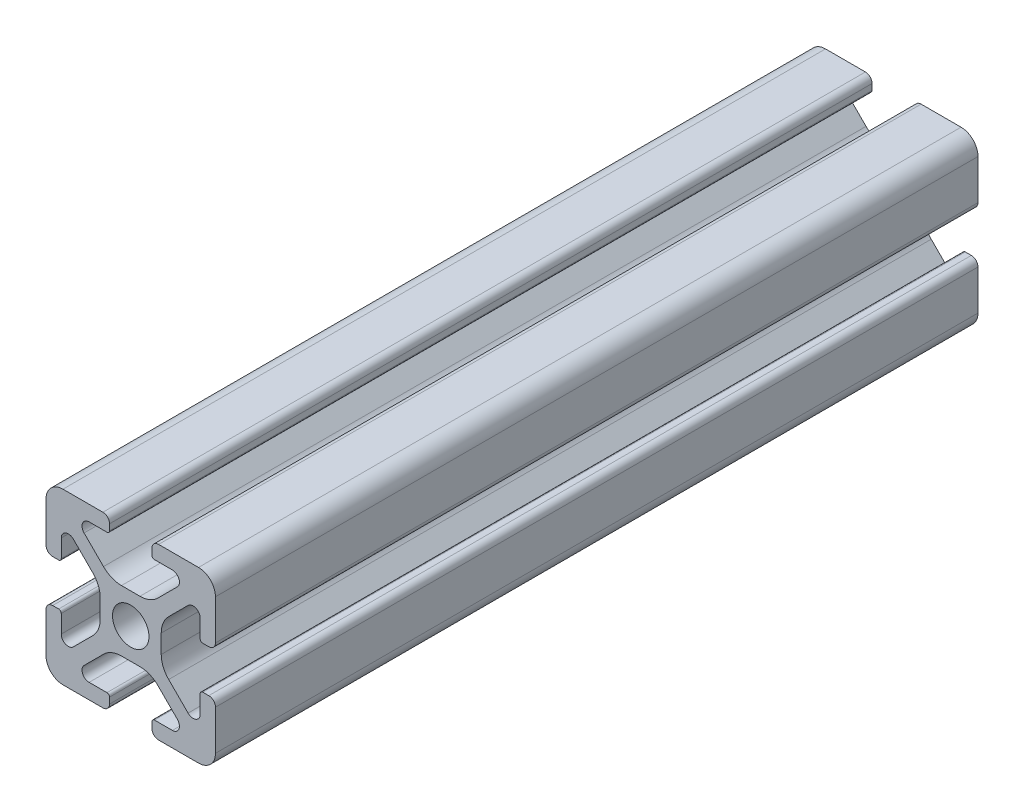
SolidWorks part; units mm, degrees
ref_plane "Front Plane" through (0, 0, 0) normal (0, 0, 1) x (1, 0, 0)
ref_plane "Top Plane" through (0, 0, 0) normal (0, 1, 0) x (1, 0, 0)
ref_plane "Right Plane" through (0, 0, 0) normal (1, 0, 0) x (0, 0, -1)
sketch "Sketch1" plane through (0, 0, 0) normal (0, 0, 1) x (1, 0, 0)
  line L0 (0, 10) -> (0, -10) construction
  line L1 (10, 0) -> (-10, 0) construction
  line L2 (-2.5, 10) -> (2.5, 10) construction
  line L3 (-5.75, 8.2) -> (5.75, 8.2) construction
  circle A0 centre (0, 0) radius 2.15 construction
  point P4 (0, 0)
  point P8 (0, 0)
  point P10 (0, 3.6)
  point P14 (0, 10)
  point P17 (0, 8.2)
  dimension "Thru Hole" = 4.3
  dimension "Height" = 20
  dimension "T Slot Depth" = 6.4
  dimension "T Slot Top Width" = 5
  dimension "T Slot Max Width" = 11.5
  dimension "Wall" = 1.8
sketch "Sketch2" plane through (0, 0, 0) normal (1, 0, 0) x (0, 0, -1)
  line L0 (45, 0) -> (-45, 0) construction
  point P4 (0, 0)
  dimension "D1" = 90
sketch "Sketch3" plane through (0, 0, 0) normal (0, 0, 1) x (1, 0, 0)
  line L0 (3.2874, 10) -> (8, 10)
  line L1 (10, 8) -> (10, -8) construction
  line L2 (8, -10) -> (-8, -10) construction
  line L3 (-10, 10) -> (10, -10) construction
  line L4 (2.5, 9.2126) -> (2.5, 8.5048)
  line L5 (-5.75, 8.2) -> (5.75, 8.2) construction
  line L6 (2.8048, 8.2) -> (4.9118, 8.2)
  line L7 (5.5045, 6.7691) -> (3.2141, 4.4787)
  line L8 (1.0928, 3.6) -> (-1.0928, 3.6)
  line L9 (0, 10) -> (0, -10) construction
  line L10 (5.75, 8.2) -> (5.75, 0) construction
  line L11 (10, 0) -> (-10, 0) construction
  line L12 (0, 0) -> (0, 10) construction
  line L13 (-2.5, 9.2126) -> (-2.5, 8.5048)
  line L14 (-5.5045, 6.7691) -> (-3.2141, 4.4787)
  line L15 (-2.8048, 8.2) -> (-4.9118, 8.2)
  line L16 (-3.2874, 10) -> (-8, 10)
  line L17 (0, 0) -> (-10, 0) construction
  line L18 (-10, 3.2874) -> (-10, 8)
  line L19 (-8.2, 2.8048) -> (-8.2, 4.9118)
  line L20 (-6.7691, 5.5045) -> (-4.4787, 3.2141)
  line L21 (-9.2126, 2.5) -> (-8.5048, 2.5)
  line L22 (-3.6, -1.0928) -> (-3.6, 1.0928)
  line L23 (-6.7691, -5.5045) -> (-4.4787, -3.2141)
  line L24 (-8.2, -2.8048) -> (-8.2, -4.9118)
  line L25 (-9.2126, -2.5) -> (-8.5048, -2.5)
  line L26 (-10, -3.2874) -> (-10, -8)
  line L27 (9.2126, -2.5) -> (8.5048, -2.5)
  line L28 (8.2, -2.8048) -> (8.2, -4.9118)
  line L29 (6.7691, -5.5045) -> (4.4787, -3.2141)
  line L30 (3.6, -1.0928) -> (3.6, 1.0928)
  line L31 (9.2126, 2.5) -> (8.5048, 2.5)
  line L32 (6.7691, 5.5045) -> (4.4787, 3.2141)
  line L33 (8.2, 2.8048) -> (8.2, 4.9118)
  line L34 (10, 8) -> (10, 3.2874)
  line L35 (10, -3.2874) -> (10, -8)
  line L36 (3.2874, -10) -> (8, -10)
  line L37 (-3.2874, -10) -> (-8, -10)
  line L38 (-6.7691, -5.5045) -> (-4.4787, -3.2141)
  line L39 (-2.8048, -8.2) -> (-4.9118, -8.2)
  line L40 (-5.5045, -6.7691) -> (-3.2141, -4.4787)
  line L41 (-2.5, -9.2126) -> (-2.5, -8.5048)
  line L42 (1.0928, -3.6) -> (-1.0928, -3.6)
  line L43 (5.5045, -6.7691) -> (3.2141, -4.4787)
  line L44 (2.8048, -8.2) -> (4.9118, -8.2)
  line L45 (2.5, -9.2126) -> (2.5, -8.5048)
  arc A0 (4.9118, 8.2) -> (5.5045, 6.7691) centre (4.9118, 7.3618) cw
  arc A1 (3.2141, 4.4787) -> (1.0928, 3.6) centre (1.0928, 6.6) cw
  circle A2 centre (0, 0) radius 2.15 construction
  circle A3 centre (0, 0) radius 2.15
  arc A4 (3.2874, 10) -> (2.5, 9.2126) centre (3.2874, 9.2126) ccw
  arc A5 (2.5, 8.5048) -> (2.8048, 8.2) centre (2.8048, 8.5048) ccw
  arc A6 (-3.2874, 10) -> (-2.5, 9.2126) centre (-3.2874, 9.2126) cw
  arc A7 (-4.9118, 8.2) -> (-5.5045, 6.7691) centre (-4.9118, 7.3618) ccw
  arc A8 (-3.2141, 4.4787) -> (-1.0928, 3.6) centre (-1.0928, 6.6) ccw
  arc A9 (-2.5, 8.5048) -> (-2.8048, 8.2) centre (-2.8048, 8.5048) cw
  arc A10 (-8.5048, 2.5) -> (-8.2, 2.8048) centre (-8.5048, 2.8048) ccw
  arc A11 (-4.4787, 3.2141) -> (-3.6, 1.0928) centre (-6.6, 1.0928) cw
  arc A12 (-8.2, 4.9118) -> (-6.7691, 5.5045) centre (-7.3618, 4.9118) cw
  arc A13 (-10, 3.2874) -> (-9.2126, 2.5) centre (-9.2126, 3.2874) ccw
  arc A14 (-8.5048, -2.5) -> (-8.2, -2.8048) centre (-8.5048, -2.8048) cw
  arc A15 (-10, -3.2874) -> (-9.2126, -2.5) centre (-9.2126, -3.2874) cw
  arc A16 (-4.4787, -3.2141) -> (-3.6, -1.0928) centre (-6.6, -1.0928) ccw
  arc A17 (-8.2, -4.9118) -> (-6.7691, -5.5045) centre (-7.3618, -4.9118) ccw
  arc A26 (-8, -10) -> (-10, -8) centre (-8, -8) cw
  arc A27 (-8, 10) -> (-10, 8) centre (-8, 8) ccw
  arc A28 (8, 10) -> (10, 8) centre (8, 8) cw
  arc A29 (10, -8) -> (8, -10) centre (8, -8) cw
  arc A30 (8.2, -4.9118) -> (6.7691, -5.5045) centre (7.3618, -4.9118) cw
  arc A31 (4.4787, -3.2141) -> (3.6, -1.0928) centre (6.6, -1.0928) cw
  arc A32 (10, -3.2874) -> (9.2126, -2.5) centre (9.2126, -3.2874) ccw
  arc A33 (8.5048, -2.5) -> (8.2, -2.8048) centre (8.5048, -2.8048) ccw
  arc A34 (10, 3.2874) -> (9.2126, 2.5) centre (9.2126, 3.2874) cw
  arc A35 (8.2, 4.9118) -> (6.7691, 5.5045) centre (7.3618, 4.9118) ccw
  arc A36 (4.4787, 3.2141) -> (3.6, 1.0928) centre (6.6, 1.0928) ccw
  arc A37 (8.5048, 2.5) -> (8.2, 2.8048) centre (8.5048, 2.8048) cw
  arc A38 (-2.5, -8.5048) -> (-2.8048, -8.2) centre (-2.8048, -8.5048) ccw
  arc A39 (-3.2141, -4.4787) -> (-1.0928, -3.6) centre (-1.0928, -6.6) cw
  arc A40 (-4.9118, -8.2) -> (-5.5045, -6.7691) centre (-4.9118, -7.3618) cw
  arc A41 (-3.2874, -10) -> (-2.5, -9.2126) centre (-3.2874, -9.2126) ccw
  arc A42 (2.5, -8.5048) -> (2.8048, -8.2) centre (2.8048, -8.5048) cw
  arc A43 (3.2874, -10) -> (2.5, -9.2126) centre (3.2874, -9.2126) cw
  arc A44 (3.2141, -4.4787) -> (1.0928, -3.6) centre (1.0928, -6.6) ccw
  arc A45 (4.9118, -8.2) -> (5.5045, -6.7691) centre (4.9118, -7.3618) ccw
  point P36 (2.5, 10)
  point P39 (2.5, 8.2)
  point P49 (0, 3.6)
  point P77 (-3.6, 0)
  point P78 (-8.2, -2.5)
  point P79 (-10, -2.5)
  point P104 (-10, -10)
  point P110 (10, 10)
  point P114 (10, -2.5)
  point P115 (8.2, -2.5)
  point P116 (3.6, 0)
  point P141 (0, -3.6)
  dimension "D1" = 3
  dimension "D2" = 0.8382
  dimension "D4" = 0.7874
  dimension "D5" = 0.3048
  dimension "D6" = 2
  dimension "D3" = 45
extrude "Boss-Extrude1" add sketch "Sketch3" along normal up to vertex (45 mm away) and the other way up to vertex (45 mm away) contours A45 L44 A42 L45 A43 L36 A29 L35 A32 L27 A33 L28 A30 L29 A31 L30 A36 L32 A35 L33 A37 L31 A34 L34 A28 L0 A4 L4 A5 L6 A0 L7 A1 L8 A8 L14 A7 L15 A9 L13 A6 L16 A27 L18 A13 L21 A10 L19 A12 L20 A11 up to point (0, 0, 45) other way up to point (0, 0, -45)
